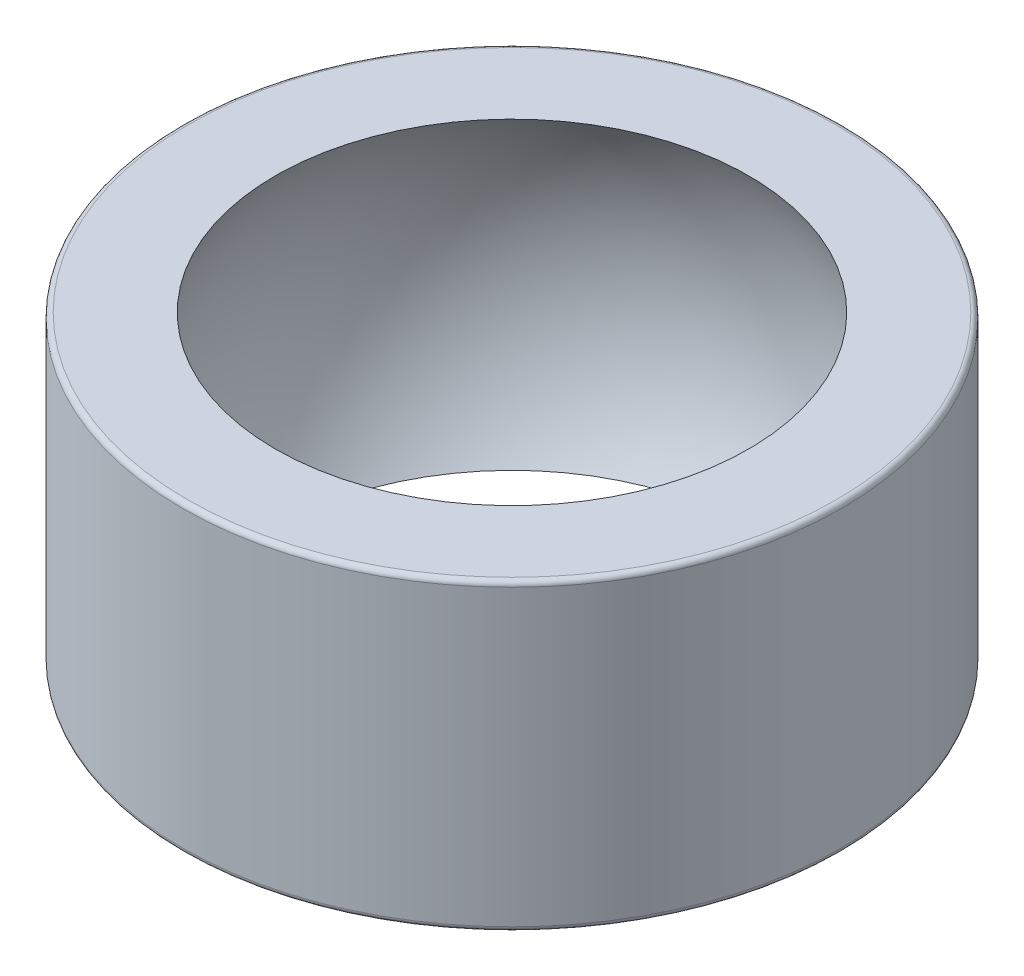
SolidWorks part; units mm, degrees
material "1.0545 (S355N)"
ref_plane "Płaszczyzna przednia" through (0, 0, 0) normal (0, 0, 1) x (1, 0, 0)
ref_plane "Płaszczyzna górna" through (0, 0, 0) normal (0, 1, 0) x (1, 0, 0)
ref_plane "Płaszczyzna prawa" through (0, 0, 0) normal (1, 0, 0) x (0, 0, -1)
sketch "Szkic1" plane through (0, 0, 0) normal (0, 1, 0) x (1, 0, 0)
  circle A0 centre (0, 0) radius 13
  dimension "d2" = 26
extrude "Dodanie-wyciągnięcie1" add sketch "Szkic1" along normal mid plane 12
sketch "Szkic3" plane through (0, 0, 0) normal (0, 0, 1) x (1, 0, 0)
  line L0 (0, -11.1) -> (0, 11.1)
  arc A0 (0, -11.1) -> (0, 11.1) centre (0, 0) ccw
  dimension "d3" = 22.2
revolve "Wycięcie-obrót1" cut sketch "Szkic3" angle 360 about L0
fillet "Zaokrąglenie1" radius 0.2 2 edges at (0, 6, 13) (0, -6, 13)
